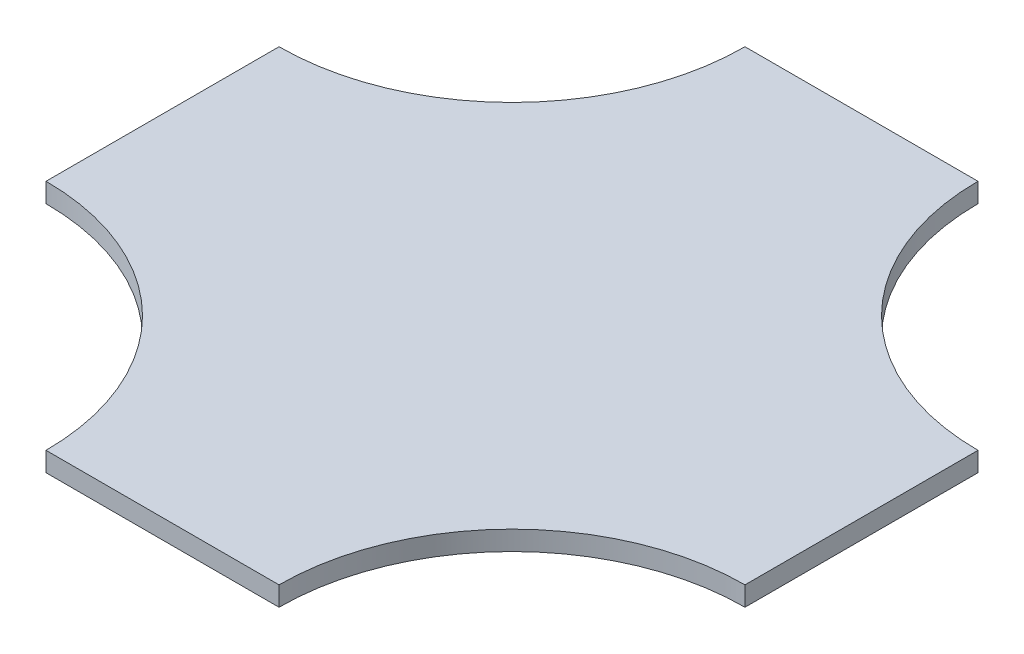
SolidWorks part; units mm, degrees
ref_plane "Front Plane" through (0, 0, 0) normal (0, 0, 1) x (1, 0, 0)
ref_plane "Top Plane" through (0, 0, 0) normal (0, 1, 0) x (1, 0, 0)
ref_plane "Right Plane" through (0, 0, 0) normal (1, 0, 0) x (0, 0, -1)
sketch "Sketch1" plane through (0, 0, 0) normal (0, 1, 0) x (1, 0, 0)
  line L0 (215.4305, 862.1306) -> (1077.1523, 862.1306) construction
  line L1 (-60, -60) -> (-60, -180)
  line L2 (60, 180) -> (-60, 180)
  line L3 (60, 180) -> (60, 60)
  line L4 (60, -180) -> (-60, -180)
  line L5 (-60, 180) -> (-60, 60)
  line L6 (-180, 60) -> (-60, 60)
  line L7 (-180, 60) -> (-180, -60)
  line L8 (-180, -60) -> (-60, -60)
  line L9 (180, 60) -> (180, -60)
  line L10 (60, -60) -> (60, -180)
  line L11 (60, 60) -> (180, 60)
  line L12 (60, -60) -> (180, -60)
  line L13 (-180, 60) -> (-180, 180) construction
  line L14 (-180, 180) -> (-60, 180) construction
  line L15 (0, 180) -> (0, -180) construction
  line L16 (-180, 0) -> (180, 0) construction
  arc A0 (-60, 180) -> (-180, 60) centre (-180, 180) cw
  arc A1 (60, 180) -> (180, 60) centre (180, 180) ccw
  arc A2 (180, -60) -> (60, -180) centre (180, -180) ccw
  arc A3 (-180, -60) -> (-60, -180) centre (-180, -180) cw
  point P19 (-180, 0)
  point P23 (0, 0)
  dimension "D1" = 120
  dimension "D2" = 180
extrude "Boss-Extrude1" add sketch "Sketch1" along normal blind 10 contours L10 L12 L9 L11 L3 L2 L5 L6 L7 L8 L1 L4 | L5 A0 L6 | A1 L3 L11 | A2 L12 L10 | L8 A3 L1
